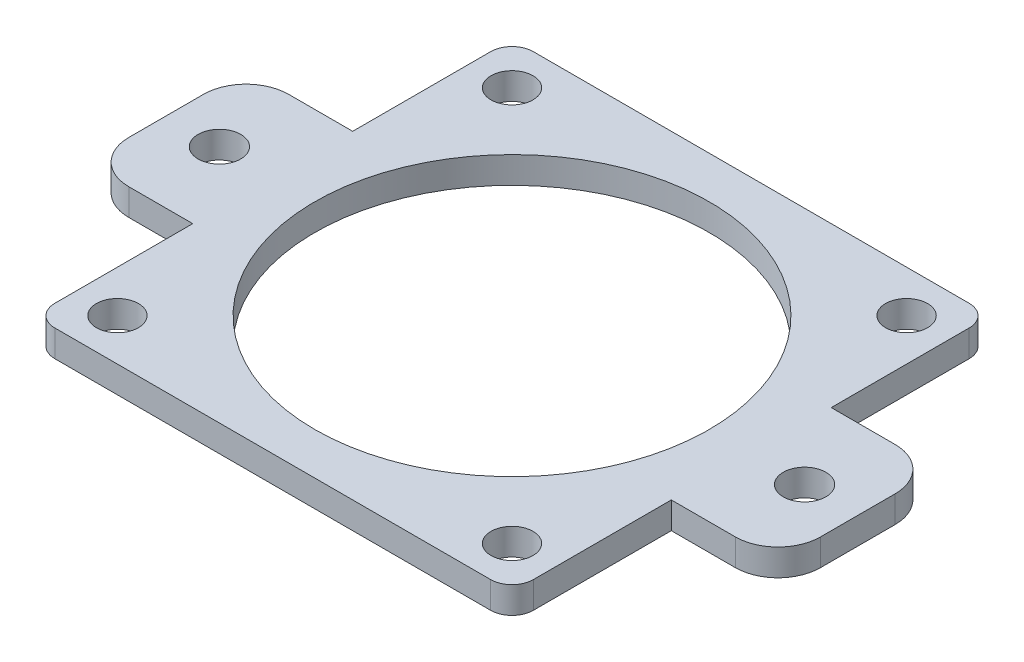
SolidWorks part; units mm, degrees
ref_plane "Front Plane" through (0, 0, 0) normal (0, 0, 1) x (1, 0, 0)
ref_plane "Top Plane" through (0, 0, 0) normal (0, 1, 0) x (1, 0, 0)
ref_plane "Right Plane" through (0, 0, 0) normal (1, 0, 0) x (0, 0, -1)
sketch "Sketch1" plane through (0, 0, 0) normal (0, 1, 0) x (1, 0, 0)
  line L0 (-13.9933, 28.5) -> (-25.96, 28.5)
  line L1 (25.96, -28.5) -> (13.9933, -28.5)
  line L2 (28.5, -25.96) -> (28.5, -13.9933)
  line L3 (25.96, 28.5) -> (13.9933, 28.5)
  line L4 (-28.5, -25.96) -> (-28.5, -13.9933)
  line L5 (28.5, -28.5) -> (-28.5, 28.5) construction
  line L6 (28.5, 28.5) -> (-28.5, -28.5) construction
  line L7 (28.5, 13.9933) -> (28.5, 25.96)
  line L8 (-13.9933, -28.5) -> (-25.96, -28.5)
  line L9 (-28.5, 13.9933) -> (-28.5, 25.96)
  line L10 (-28.5, 13.9933) -> (-28.5, 9.525)
  line L11 (-13.9933, -28.5) -> (13.9933, -28.5)
  line L12 (-13.9933, 28.5) -> (13.9933, 28.5)
  line L13 (28.5, 13.9933) -> (28.5, 9.525)
  line L14 (-28.5, -9.525) -> (-28.5, -13.9933)
  line L15 (-28.5, -9.525) -> (-36.12, -9.525)
  line L17 (-28.5, 9.525) -> (-36.12, 9.525)
  line L18 (-41.2, -4.445) -> (-41.2, 4.445)
  line L19 (-13.9933, -28.5) -> (-51.9125, -28.5) construction
  line L20 (-13.9933, 28.5) -> (-51.9125, 28.5) construction
  line L21 (-41.2, 9.525) -> (-41.2, 28.5) construction
  line L22 (-41.2, -9.525) -> (-41.2, -28.5) construction
  line L23 (0, -28.5) -> (0, 28.5) construction
  line L24 (28.5, -9.525) -> (36.12, -9.525)
  line L25 (41.2, -4.445) -> (41.2, 4.445)
  line L26 (28.5, 9.525) -> (36.12, 9.525)
  line L27 (28.5, -9.525) -> (28.5, -13.9933)
  circle A0 centre (0, 0) radius 23.495
  arc A5 (-25.96, -28.5) -> (-28.5, -25.96) centre (-25.96, -25.96) cw
  arc A6 (25.96, -28.5) -> (28.5, -25.96) centre (25.96, -25.96) ccw
  arc A7 (28.5, 25.96) -> (25.96, 28.5) centre (25.96, 25.96) ccw
  arc A8 (-25.96, 28.5) -> (-28.5, 25.96) centre (-25.96, 25.96) ccw
  circle A9 centre (-23.5, 23.5) radius 2.5
  circle A10 centre (23.5, 23.5) radius 2.5
  circle A11 centre (23.5, -23.5) radius 2.5
  circle A12 centre (-23.5, -23.5) radius 2.5
  circle A13 centre (-34.85, 0) radius 2.54
  arc A14 (36.12, -9.525) -> (41.2, -4.445) centre (36.12, -4.445) ccw
  arc A15 (41.2, 4.445) -> (36.12, 9.525) centre (36.12, 4.445) ccw
  arc A16 (-36.12, 9.525) -> (-41.2, 4.445) centre (-36.12, 4.445) ccw
  arc A17 (-36.12, -9.525) -> (-41.2, -4.445) centre (-36.12, -4.445) cw
  circle A18 centre (34.85, 0) radius 2.54
  point P9 (-28.5, 0)
  point P38 (0, 0)
  point P55 (41.2, -9.525)
  point P58 (41.2, 9.525)
  dimension "D1" = 19.05
  dimension "D4" = 2.54
  dimension "D5" = 46.99
  dimension "D6" = 5
  dimension "D10" = 6.35
  dimension "D12" = 5.08
  dimension "D13" = 5.08
  dimension "D2" = 57
  dimension "D3" = 57
  dimension "D7" = 5
  dimension "D9" = 12.7
  dimension "D11" = 9.525
  dimension "D8" = 4
extrude "Boss-Extrude1" add sketch "Sketch1" along normal blind 3.175
